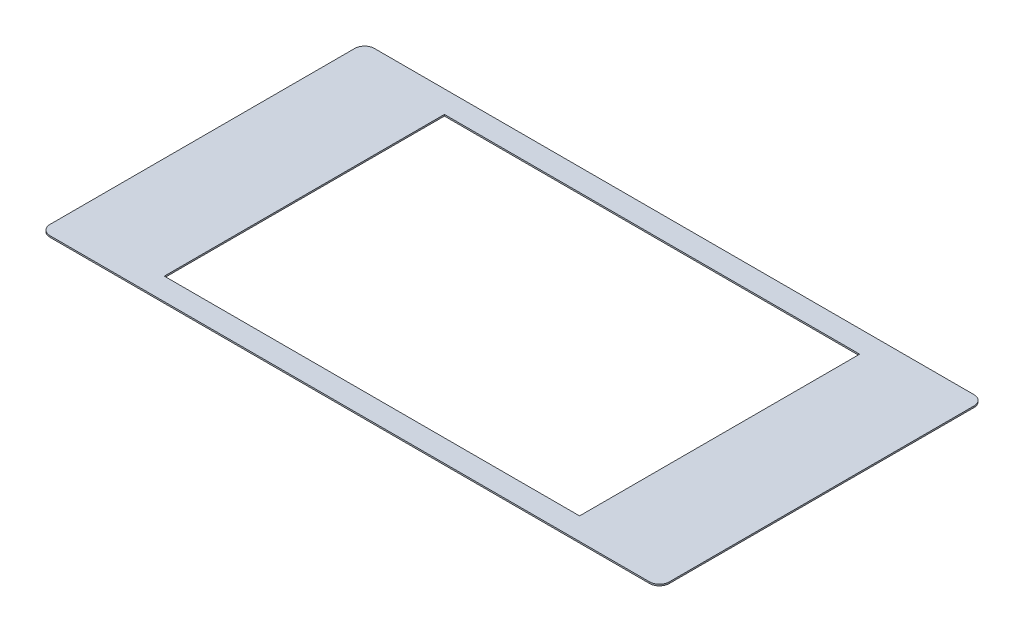
SolidWorks part; units mm, degrees
ref_plane "Front Plane" through (0, 0, 0) normal (0, 0, 1) x (1, 0, 0)
ref_plane "Top Plane" through (0, 0, 0) normal (0, 1, 0) x (1, 0, 0)
ref_plane "Right Plane" through (0, 0, 0) normal (1, 0, 0) x (0, 0, -1)
sketch "Sketch1" plane through (0, -34.5, 0) normal (0, -1, 0) x (1, 0, 0)
  line L1 (-63, 33) -> (63, 33)
  line L2 (-63, 33) -> (-63, -33)
  line L3 (-63, -33) -> (63, -33)
  line L4 (63, 33) -> (63, -33)
  line L5 (-63, 33) -> (63, -33) construction
  line L6 (-63, -33) -> (63, 33) construction
  line L9 (-42.25, 28.5) -> (42.25, 28.5)
  line L10 (-42.25, 28.5) -> (-42.25, -28.5)
  line L11 (-42.25, -28.5) -> (42.25, -28.5)
  line L12 (42.25, 28.5) -> (42.25, -28.5)
  line L13 (-42.25, 28.5) -> (42.25, -28.5) construction
  line L14 (-42.25, -28.5) -> (42.25, 28.5) construction
  point P0 (0, 0)
  point P8 (0, 0)
  point P10 (0, 0)
  point P16 (0, 0)
  point P17 (0, 0)
  point P18 (0, 0)
  point P19 (0, 0)
  dimension "D1" = 126
  dimension "D2" = 66
extrude "Boss-Extrude1" add sketch "Sketch1" along normal blind 0.3
fillet "Fillet1" radius 2 4 edges at (-63, -34.65, 33) (-63, -34.65, -33) (63, -34.65, -33) (63, -34.65, 33)
